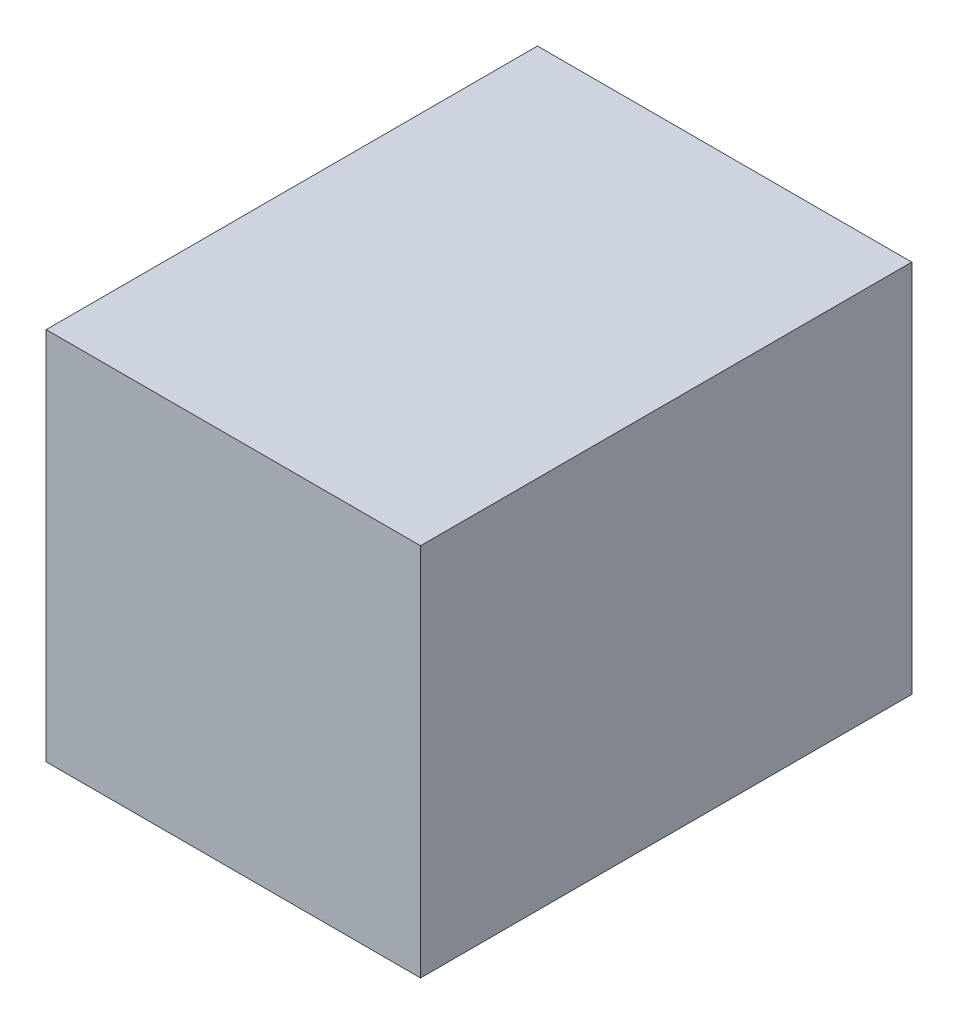
SolidWorks part; units mm, degrees
ref_plane "Front Plane" through (0, 0, 0) normal (0, 0, 1) x (1, 0, 0)
ref_plane "Top Plane" through (0, 0, 0) normal (0, 1, 0) x (1, 0, 0)
ref_plane "Right Plane" through (0, 0, 0) normal (1, 0, 0) x (0, 0, -1)
sketch "Sketch1" plane through (0, 0, 0) normal (0, 0, 1) x (1, 0, 0)
  line L1 (-381, -381) -> (381, -381)
  line L2 (-381, -381) -> (-381, 381)
  line L3 (-381, 381) -> (381, 381)
  line L4 (381, -381) -> (381, 381)
  line L5 (-381, -381) -> (381, 381) construction
  line L6 (-381, 381) -> (381, -381) construction
  point P0 (0, 0)
  dimension "D1" = 762
  dimension "D2" = 762
extrude "Boss-Extrude1" add sketch "Sketch1" along normal blind 1000
